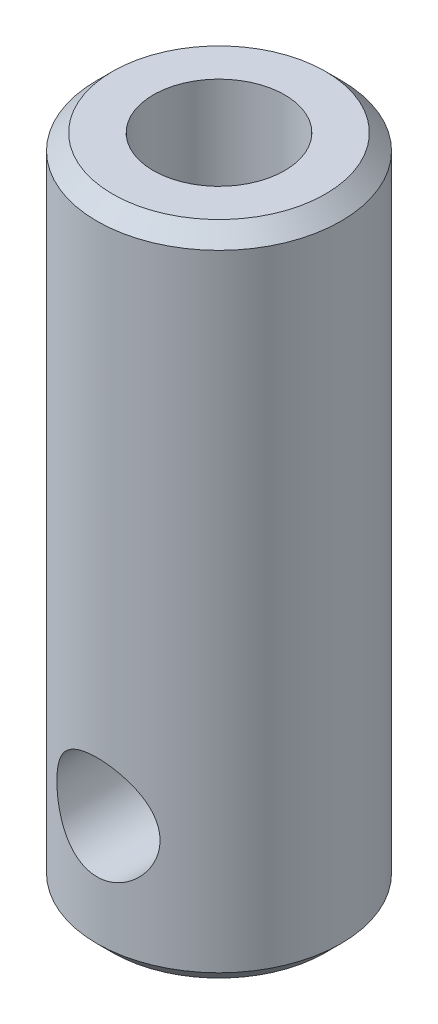
SolidWorks part; units mm, degrees
material "6061 合金"
ref_plane "前视基准面" through (0, 0, 0) normal (0, 0, 1) x (1, 0, 0)
ref_plane "上视基准面" through (0, 0, 0) normal (0, 1, 0) x (1, 0, 0)
ref_plane "右视基准面" through (0, 0, 0) normal (1, 0, 0) x (0, 0, -1)
sketch "草图1" plane through (0, 0, 0) normal (0, 1, 0) x (1, 0, 0)
  circle A0 centre (0, 0) radius 3.9
  dimension "D1" = 7.8
extrude "凸台-拉伸1" add sketch "草图1" along normal blind 21
ref_plane "基准面1" through (0, 0, 3.9) normal (0, 0, 1) x (1, 0, 0)
hole_wizard "M4 螺纹孔1" positions "草图2" profile "草图3" tap size "M4" standard "GB" end condition through all
sketch "草图2" plane through (0, 0, 3.9) normal (0, 0, 1) x (1, 0, 0)
  line L0 (-3.9, 0) -> (3.9, 0) construction
  point P0 (0, 4)
  dimension "D1" = 4
sketch "草图3" plane through (0, 4, 3.9) normal (1, 0, 0) x (0, -1, 0)
  line L0 (0, 0) -> (0, 7.8)
  line L1 (0, 7.8) -> (1.65, 7.8)
  line L2 (1.65, 7.8) -> (1.65, 0)
  line L5 (1.65, 0) -> (0, 0)
  line L11 (0, -6.35) -> (0, 107.95) construction
  dimension "通孔螺纹孔钻头直径" = 3.3
  dimension "通孔螺纹孔钻头深度" = 7.8
cosmetic thread "孔螺蚊线1"
hole_wizard "M5 螺纹孔1" positions "草图4" profile "草图5" tap size "M5" standard "GB"
sketch "草图4" plane through (0, 21, 0) normal (0, 1, 0) x (1, 0, 0)
  point P0 (0, 0)
cosmetic thread "孔螺蚊线2"
sketch "草图5" plane through (0, 21, 0) normal (1, 0, 0) x (0, 0, 1)
  line L0 (0, 0) -> (0, 13.2618)
  line L1 (0, 13.2618) -> (2.1, 12)
  line L2 (2.1, 12) -> (2.1, 0)
  line L5 (2.1, 0) -> (0, 0)
  line L10 (0, 13.2618) -> (-2.1, 12) construction
  line L11 (0, -6.35) -> (0, 107.95) construction
  dimension "螺纹孔钻头直径" = 4.2
  dimension "螺纹孔钻头深度" = 12
  dimension "导头角度" = 118
chamfer "倒角1" distance 0.5 angle 45 2 edges at (0, 0, 3.9) (0, 21, 3.9)
